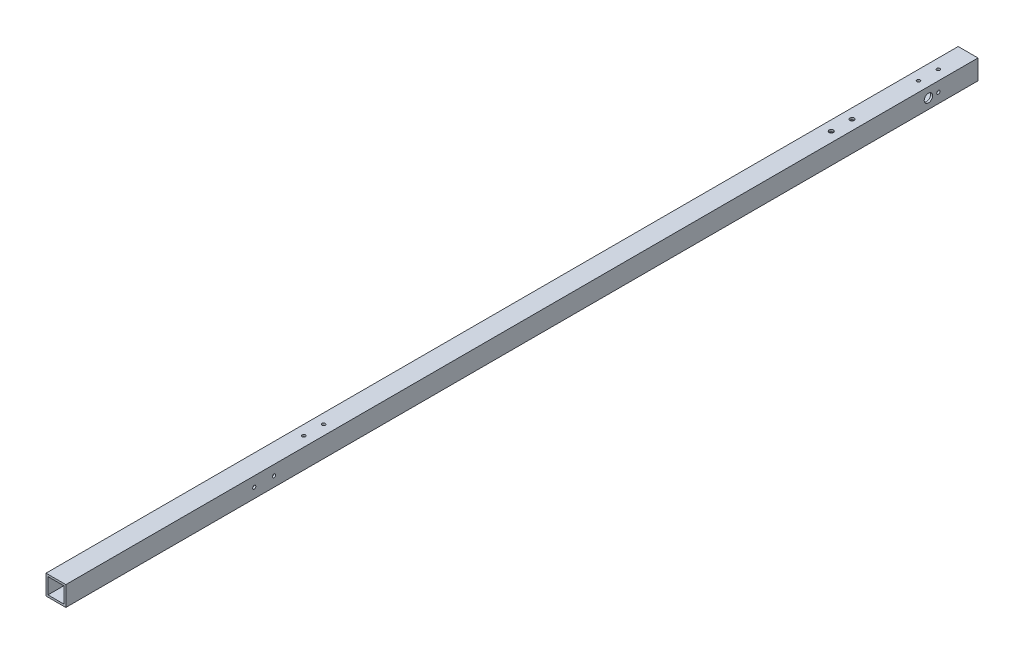
SolidWorks part; units mm, degrees
ref_plane "正面" through (0, 0, 0) normal (0, 0, 1) x (1, 0, 0)
ref_plane "平面" through (0, 0, 0) normal (0, 1, 0) x (1, 0, 0)
ref_plane "右側面" through (0, 0, 0) normal (1, 0, 0) x (0, 0, -1)
sketch "ｽｹｯﾁ1" plane through (0, 0, 0) normal (0, 0, 1) x (1, 0, 0)
  line L1 (-10, 10) -> (10, 10)
  line L2 (-10, 10) -> (-10, -10)
  line L3 (-10, -10) -> (10, -10)
  line L4 (10, 10) -> (10, -10)
  line L5 (-10, 10) -> (10, -10) construction
  line L6 (-10, -10) -> (10, 10) construction
  line L7 (-8, 8) -> (8, 8)
  line L8 (-8, 8) -> (-8, -8)
  line L9 (-8, -8) -> (8, -8)
  line L10 (8, 8) -> (8, -8)
  line L11 (-8, 8) -> (8, -8) construction
  line L12 (-8, -8) -> (8, 8) construction
  point P0 (0, 0)
  point P6 (0, 0)
  dimension "D1" = 20
  dimension "D2" = 20
  dimension "D3" = 16
  dimension "D4" = 16
extrude "ﾎﾞｽ - 押し出し1" add sketch "ｽｹｯﾁ1" along normal blind 970
sketch "ｽｹｯﾁ2" plane through (10, 0, 0) normal (1, 0, 0) x (0, 0, -1)
  line L0 (-970, 0) -> (-710, 0)
  line L1 (-970, -10) -> (-970, 10) construction
  line L2 (-710, 0) -> (-890.4665, 0)
  line L3 (-890.4665, 0) -> (-845.8821, 0)
  line L4 (-845.8821, 0) -> (-803.5394, 0)
  line L5 (-710, 0) -> (-670, 0)
  line L6 (-670, 0) -> (-50, 0)
  line L7 (-50, 0) -> (-40, 0)
  line L8 (-710, 0) -> (-730, 0)
  circle A0 centre (-710, 0) radius 1
  circle A4 centre (-670, 0) radius 2.1
  circle A5 centre (-50, 0) radius 4.25
  circle A6 centre (-40, 0) radius 1
  circle A7 centre (-730, 0) radius 1
  dimension "D5" = 2
  dimension "D6" = 8.5
  dimension "D7" = 4.2
  dimension "D8" = 2
  dimension "D10" = 2
  dimension "D1" = 260
  dimension "D2" = 40
  dimension "D3" = 620
  dimension "D4" = 10
  dimension "D9" = 20
extrude "ｶｯﾄ - 押し出し1" cut sketch "ｽｹｯﾁ2" against normal blind 10
sketch "ｽｹｯﾁ3" plane through (0, 10, 0) normal (0, 1, 0) x (1, 0, 0)
  line L0 (0, -970) -> (0, -690)
  line L1 (10, -970) -> (-10, -970) construction
  line L2 (0, -690) -> (0, -670)
  line L3 (0, -670) -> (0, -10)
  line L4 (0, -670) -> (0, -650)
  circle A0 centre (0, -690) radius 2.2
  circle A1 centre (0, -670) radius 1
  circle A2 centre (0, -10) radius 2.2
  circle A3 centre (0, -650) radius 1
  dimension "D2" = 4.4
  dimension "D4" = 2
  dimension "D6" = 4.4
  dimension "D7" = 2
  dimension "D1" = 280
  dimension "D3" = 20
  dimension "D5" = 20
extrude "ｶｯﾄ - 押し出し2" cut sketch "ｽｹｯﾁ3" against normal blind 10 contours L3 A3 | L3 A3 | L2 A1 L3 | L3 A1 L2
sketch "ｽｹｯﾁ5" plane through (0, 10, 0) normal (0, 1, 0) x (1, 0, 0)
  line L0 (0, 0) -> (0, -117)
  line L1 (0, -117) -> (0, -138)
  circle A0 centre (0, -117) radius 2.2
  circle A1 centre (0, -138) radius 2.2
  dimension "D2" = 4.4
  dimension "D4" = 4.4
  dimension "D1" = 117
  dimension "D3" = 21
extrude "ｶｯﾄ - 押し出し7" cut sketch "ｽｹｯﾁ5" against normal blind 30
sketch "ｽｹｯﾁ6" plane through (0, 0, 970) normal (0, 0, 1) x (1, 0, 0)
  line L1 (13.9129, -10.9209) -> (-13.9129, -10.9209)
  line L2 (13.9129, -10.9209) -> (13.9129, 10.9209)
  line L3 (13.9129, 10.9209) -> (-13.9129, 10.9209)
  line L4 (-13.9129, -10.9209) -> (-13.9129, 10.9209)
  line L5 (13.9129, -10.9209) -> (-13.9129, 10.9209) construction
  line L6 (13.9129, 10.9209) -> (-13.9129, -10.9209) construction
  point P0 (0, 0)
extrude "ｶｯﾄ - 押し出し8" cut sketch "ｽｹｯﾁ6" against normal blind 50
sketch "ｽｹｯﾁ7" plane through (0, -10, 0) normal (0, -1, 0) x (-1, 0, 0)
  line L0 (0, 0) -> (0, -10)
  line L1 (0, -10) -> (0, -30)
  line L2 (0, -30) -> (0, -50)
  circle A0 centre (0, -30) radius 1
  circle A1 centre (0, -50) radius 1
  dimension "D4" = 2
  dimension "D5" = 2
  dimension "D1" = 10
  dimension "D2" = 20
  dimension "D3" = 20
hole_wizard "M4x0.7 ねじ穴3" positions "3Dｽｹｯﾁ3" profile "ｽｹｯﾁ10" tap size "M4x0.7" standard "JIS"
sketch3d "3Dｽｹｯﾁ3"
  line L0 (0, 8, 650) -> (0, 10, 650) construction
  line L1 (0, 8, 670) -> (0, 10, 670) construction
  point P0 (0, 10, 650)
  point P4 (0, 10, 670)
sketch "ｽｹｯﾁ10" plane through (0, 10, 650) normal (1, 0, 0) x (0, 0, 1)
  line L0 (0, 0) -> (0, 12.4914)
  line L1 (0, 12.4914) -> (1.65, 11.5)
  line L2 (1.65, 11.5) -> (1.65, 0)
  line L5 (1.65, 0) -> (0, 0)
  line L10 (0, 12.4914) -> (-1.65, 11.5) construction
  line L11 (0, -6.35) -> (0, 107.95) construction
  dimension "ねじ下穴ﾄﾞﾘﾙ直径" = 3.3
  dimension "ねじ下穴ﾄﾞﾘﾙの深さ" = 11.5
  dimension "ﾄﾞﾘﾙ角度" = 118
cosmetic thread "穴のねじ山4" parameters "D1"=2, "D2"=4
cosmetic thread "穴のねじ山5" parameters "D1"=2, "D2"=4
sketch "ｽｹｯﾁ11" plane through (0, 10, 0) normal (0, 1, 0) x (1, 0, 0)
  line L0 (0, 0) -> (0, -30)
  line L1 (10, 0) -> (-10, 0) construction
  line L2 (0, -30) -> (0, -50)
  circle A0 centre (0, -30) radius 1
  circle A1 centre (0, -50) radius 1
  dimension "D3" = 2
  dimension "D4" = 2
  dimension "D1" = 30
  dimension "D2" = 20
extrude "ｶｯﾄ - 押し出し9" cut sketch "ｽｹｯﾁ11" against normal blind 10
hole_wizard "M4x0.7 ねじ穴4" positions "3Dｽｹｯﾁ4" profile "ｽｹｯﾁ12" tap size "M4x0.7" standard "JIS"
sketch3d "3Dｽｹｯﾁ4"
  line L0 (0, 8, 30) -> (0, 10, 30) construction
  line L1 (0, 8, 50) -> (0, 10, 50) construction
  point P0 (0, 10, 30)
  point P4 (0, 10, 50)
sketch "ｽｹｯﾁ12" plane through (0, 10, 30) normal (1, 0, 0) x (0, 0, 1)
  line L0 (0, 0) -> (0, 12.4914)
  line L1 (0, 12.4914) -> (1.65, 11.5)
  line L2 (1.65, 11.5) -> (1.65, 0)
  line L5 (1.65, 0) -> (0, 0)
  line L10 (0, 12.4914) -> (-1.65, 11.5) construction
  line L11 (0, -6.35) -> (0, 107.95) construction
  dimension "ねじ下穴ﾄﾞﾘﾙ直径" = 3.3
  dimension "ねじ下穴ﾄﾞﾘﾙの深さ" = 11.5
  dimension "ﾄﾞﾘﾙ角度" = 118
cosmetic thread "穴のねじ山6" parameters "D1"=2, "D2"=4
cosmetic thread "穴のねじ山7" parameters "D1"=2, "D2"=4
sketch "ｽｹｯﾁ13" plane through (10, 0, 0) normal (1, 0, 0) x (0, 0, -1)
  circle A0 centre (-50, 0) radius 4.25
extrude "ｶｯﾄ - 押し出し10" cut sketch "ｽｹｯﾁ13" against normal through all
hole_wizard "M4x0.7 ねじ穴5" positions "3Dｽｹｯﾁ5" profile "ｽｹｯﾁ14" tap size "M4x0.7" standard "JIS"
sketch3d "3Dｽｹｯﾁ5"
  line L0 (8, 0, 40) -> (10, 0, 40) construction
  line L1 (8, 0, 710) -> (10, 0, 710) construction
  line L2 (8, 0, 730) -> (10, 0, 730) construction
  point P0 (10, 0, 40)
  point P4 (10, 0, 710)
  point P8 (10, 0, 730)
sketch "ｽｹｯﾁ14" plane through (10, 0, 40) normal (0, 1, 0) x (0, 0, -1)
  line L0 (0, 0) -> (0, 12.4914)
  line L1 (0, 12.4914) -> (1.65, 11.5)
  line L2 (1.65, 11.5) -> (1.65, 0)
  line L5 (1.65, 0) -> (0, 0)
  line L10 (0, 12.4914) -> (-1.65, 11.5) construction
  line L11 (0, -6.35) -> (0, 107.95) construction
  dimension "ねじ下穴ﾄﾞﾘﾙ直径" = 3.3
  dimension "ねじ下穴ﾄﾞﾘﾙの深さ" = 11.5
  dimension "ﾄﾞﾘﾙ角度" = 118
cosmetic thread "穴のねじ山8" parameters "D1"=2, "D2"=4
cosmetic thread "穴のねじ山9" parameters "D1"=2, "D2"=4
cosmetic thread "穴のねじ山10" parameters "D1"=2, "D2"=4
